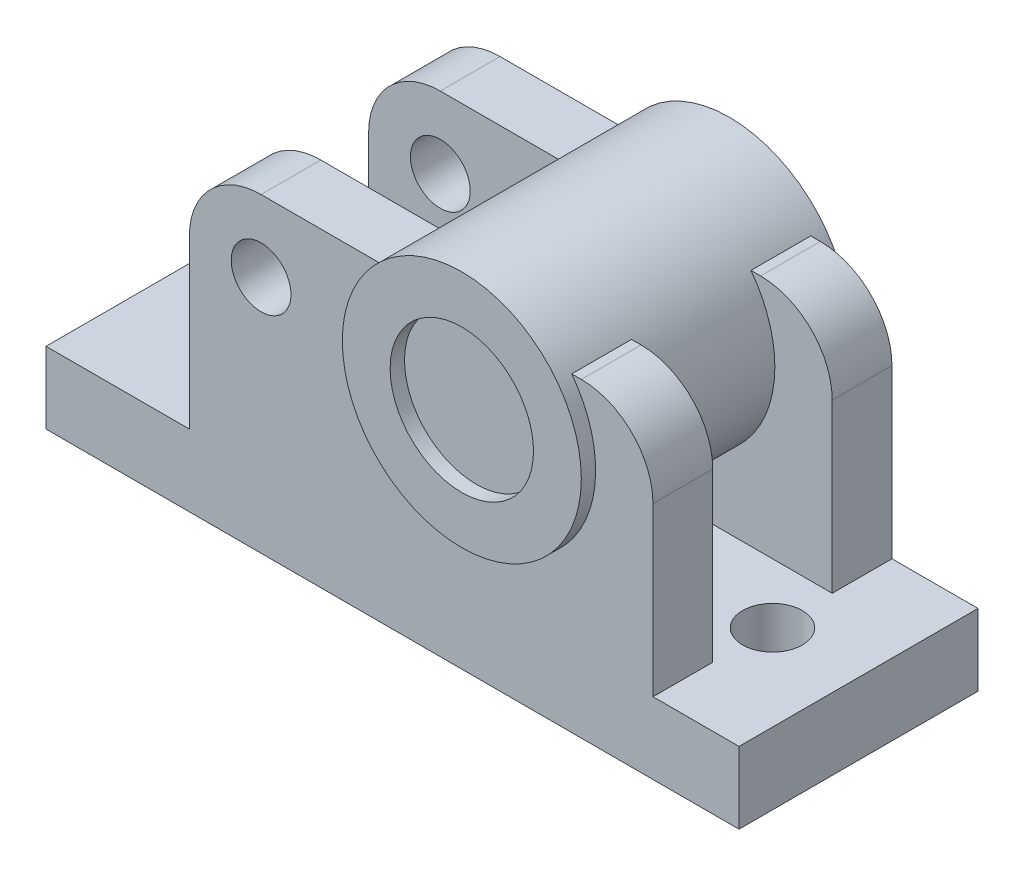
SolidWorks part; units mm, degrees
ref_plane "Front Plane" through (0, 0, 0) normal (0, 0, 1) x (1, 0, 0)
ref_plane "Top Plane" through (0, 0, 0) normal (0, 1, 0) x (1, 0, 0)
ref_plane "Right Plane" through (0, 0, 0) normal (1, 0, 0) x (0, 0, -1)
sketch "Sketch1" plane through (0, 0, 0) normal (0, 0, 1) x (1, 0, 0)
  line L1 (0, 0) -> (290, 0)
  line L2 (0, 0) -> (0, 30)
  line L3 (0, 30) -> (290, 30)
  line L4 (290, 0) -> (290, 30)
  dimension "D1" = 30
  dimension "D2" = 290
extrude "Boss-Extrude1" add sketch "Sketch1" along normal mid plane 100
sketch "Sketch5" plane through (0, 0, 0) normal (0, 1, 0) x (1, 0, 0)
  line L0 (145, 54.9419) -> (145, -71.6169) construction
  line L1 (0, -50) -> (0, 50) construction
  line L2 (290, -50) -> (0, -50) construction
  circle A0 centre (36, 0) radius 12.5
  circle A1 centre (254, 0) radius 12.5
  dimension "D3" = 25
  dimension "D1" = 145
  dimension "D2" = 36
  dimension "D4" = 50
extrude "Cut-Extrude3" cut sketch "Sketch5" along normal up to next contours A0 | A1
sketch "Sketch7" plane through (0, 0, 50) normal (0, 0, 1) x (1, 0, 0)
  line L0 (290, 30) -> (0, 30) construction
  line L1 (254, 30) -> (60, 30)
  line L2 (60, 30) -> (60, 130)
  line L3 (60, 130) -> (254, 130)
  line L4 (254, 130) -> (254, 30)
  line L5 (0, 30) -> (0, 0) construction
  line L6 (290, 0) -> (290, 30) construction
  circle A0 centre (90, 100) radius 12.5
  point P14 (60, 91.3499)
  point P15 (60, 95.8464)
  dimension "D4" = 25
  dimension "D1" = 60
  dimension "D2" = 36
  dimension "D3" = 100
  dimension "D5" = 30
  dimension "D6" = 30
extrude "Boss-Extrude2" add sketch "Sketch7" against normal blind 25
fillet "Fillet1" radius 30 2 edges at (254, 130, 37.5) (60, 130, 37.5)
sketch "Sketch8" plane through (0, 0, -50) normal (0, 0, -1) x (-1, 0, 0)
  line L4 (-90, 130) -> (-224, 130)
  line L5 (-254, 100) -> (-254, 30)
  line L6 (-254, 30) -> (-60, 30)
  line L7 (-60, 30) -> (-60, 100)
  line L8 (-90, 130) -> (-224, 130)
  line L9 (-254, 100) -> (-254, 30)
  line L10 (-254, 30) -> (-60, 30)
  line L11 (-60, 30) -> (-60, 100)
  circle A0 centre (-90, 100) radius 12.5 construction
  circle A1 centre (-90, 100) radius 12.5
  arc A2 (-224, 130) -> (-254, 100) centre (-224, 100) ccw
  arc A3 (-60, 100) -> (-90, 130) centre (-90, 100) ccw
  arc A4 (-224, 130) -> (-254, 100) centre (-224, 100) ccw
  arc A5 (-60, 100) -> (-90, 130) centre (-90, 100) ccw
  dimension "D1" = 0
extrude "Boss-Extrude3" add sketch "Sketch8" against normal blind 25
sketch "Sketch9" plane through (0, 0, 0) normal (0, 0, 1) x (1, 0, 0)
  line L0 (0, 30) -> (0, 0) construction
  line L3 (60, 30) -> (0, 30) construction
  circle A0 centre (180, 100) radius 50
  circle A1 centre (180, 100) radius 30
  dimension "D1" = 100
  dimension "D2" = 60
  dimension "D3" = 180
  dimension "D4" = 70
extrude "Boss-Extrude4" add sketch "Sketch9" along normal mid plane 112
